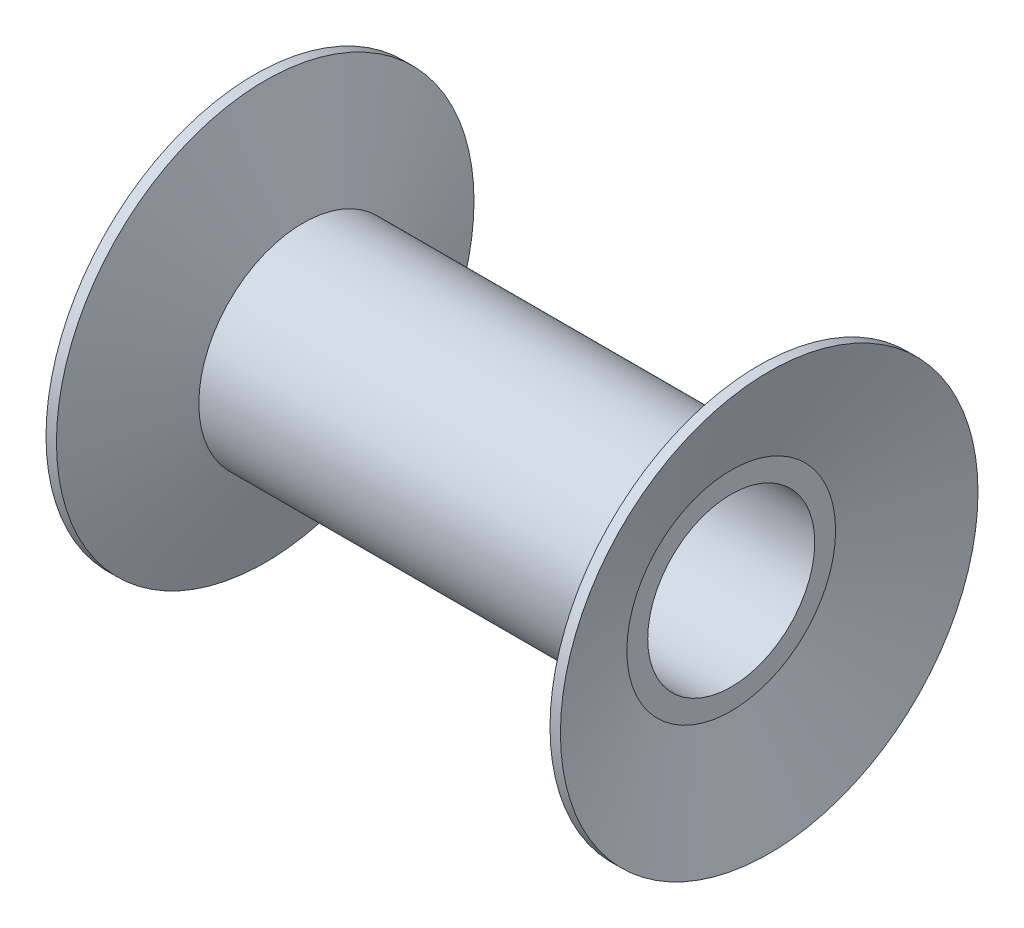
SolidWorks part; units mm, degrees
ref_plane "Front Plane" through (0, 0, 0) normal (0, 0, 1) x (1, 0, 0)
ref_plane "Top Plane" through (0, 0, 0) normal (0, 1, 0) x (1, 0, 0)
ref_plane "Right Plane" through (0, 0, 0) normal (1, 0, 0) x (0, 0, -1)
sketch "Sketch3" plane through (0, 0, 0) normal (0, 0, 1) x (1, 0, 0)
  line L0 (100, 50) -> (-100, 50)
  line L1 (0, -69.4075) -> (0, 69.4075) construction
  line L2 (-100, 50) -> (-118.1985, 100)
  line L3 (-118.1985, 100) -> (-123.1985, 100)
  line L4 (-123.1985, 100) -> (-105, 50)
  line L5 (-105, 50) -> (-105, 0)
  line L6 (151.1175, 0) -> (-151.1175, 0) construction
  line L7 (-105, 0) -> (105, 0)
  line L8 (0, 47.3583) -> (0, -26.3036) construction
  line L9 (105, 50) -> (105, 0)
  line L10 (118.1985, 100) -> (123.1985, 100)
  line L11 (123.1985, 100) -> (105, 50)
  line L12 (100, 50) -> (118.1985, 100)
  line L13 (-146.7966, 0) -> (145.7597, 0) construction
  point P15 (0, 0)
  point P17 (0, 50)
  dimension "D1" = 200
  dimension "D2" = 50
  dimension "D3" = 50
  dimension "D4" = 160
  dimension "D5" = 5
  dimension "D6" = 50
ref_axis "Axis1" through (160.3875, 0, 0) along (-1, 0, 0)
revolve "Revolve1" add sketch "Sketch3" angle 360 about axis through (160.3875, 0, 0) along (-1, 0, 0)
sketch "Sketch4" plane through (0, 0, 0) normal (1, 0, 0) x (0, 0, -1)
  circle A0 centre (0, 0) radius 40
  circle A1 centre (0, 0) radius 50 construction
  dimension "D1" = 10
extrude "Cut-Extrude2" cut sketch "Sketch4" against normal through all and the other way through all
